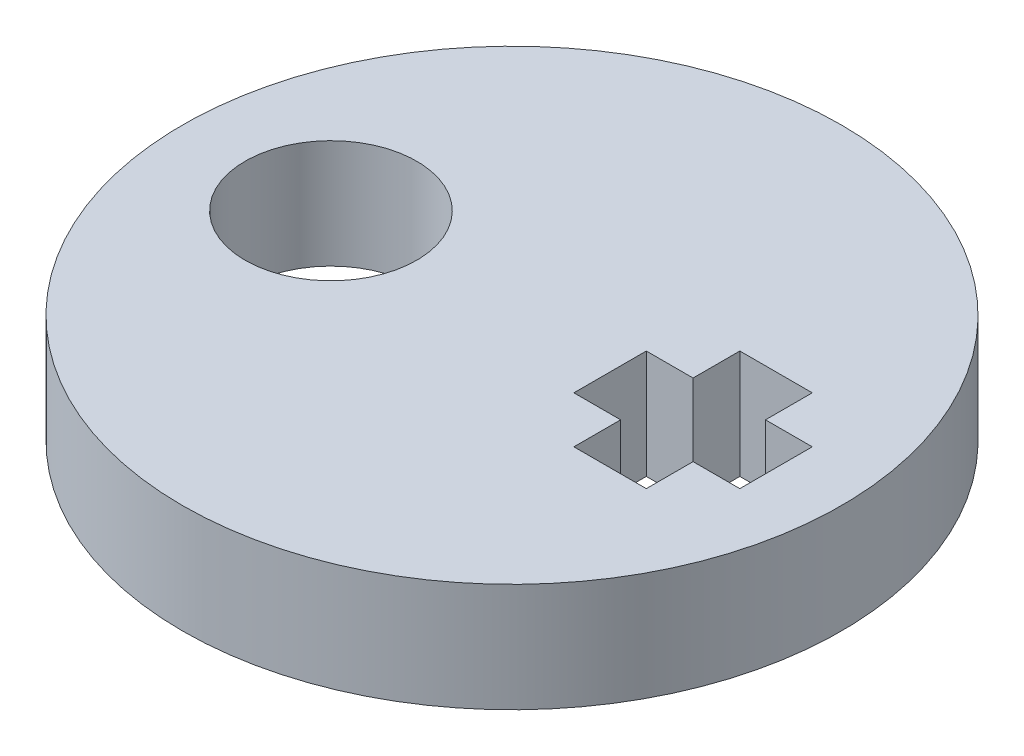
SolidWorks part; units mm, degrees
ref_plane "Front Plane" through (0, 0, 0) normal (0, 0, 1) x (1, 0, 0)
ref_plane "Top Plane" through (0, 0, 0) normal (0, 1, 0) x (1, 0, 0)
ref_plane "Right Plane" through (0, 0, 0) normal (1, 0, 0) x (0, 0, -1)
sketch "Sketch1" plane through (0, 0, 0) normal (0, 1, 0) x (1, 0, 0)
  line L0 (7.2913, -1) -> (6, -1)
  line L1 (7.2913, 1) -> (7.2913, -1)
  line L2 (6, 1) -> (7.2913, 1)
  line L3 (6, 2.2913) -> (6, 1)
  line L4 (4, 2.2913) -> (6, 2.2913)
  line L5 (4, 1) -> (4, 2.2913)
  line L6 (2.7087, 1) -> (4, 1)
  line L7 (2.7087, -1) -> (2.7087, 1)
  line L8 (4, -1) -> (2.7087, -1)
  line L9 (4, -2.2913) -> (4, -1)
  line L10 (6, -2.2913) -> (4, -2.2913)
  line L11 (6, -1) -> (6, -2.2913)
  line L12 (2.7087, 0) -> (7.2863, 0) construction
  line L13 (5, 2.2913) -> (5, -2.2913) construction
  circle A0 centre (0, 0) radius 9.1
  circle A3 centre (-5, 0) radius 2.37
  point P19 (2.7087, 0)
  dimension "D1" = 18.2
  dimension "D3" = 4.74
  dimension "D5" = 5
  dimension "D7" = 1.2913
  dimension "D2" = 5
  dimension "D4" = 4.5826
  dimension "D6" = 3.2913
  dimension "D8" = 1.2913
  dimension "D9" = 1.2913
  dimension "D10" = 1.2913
  dimension "D11" = 2
  dimension "D12" = 2
  dimension "D13" = 2
  dimension "D14" = 2
extrude "Boss-Extrude1" add sketch "Sketch1" along normal blind 3
